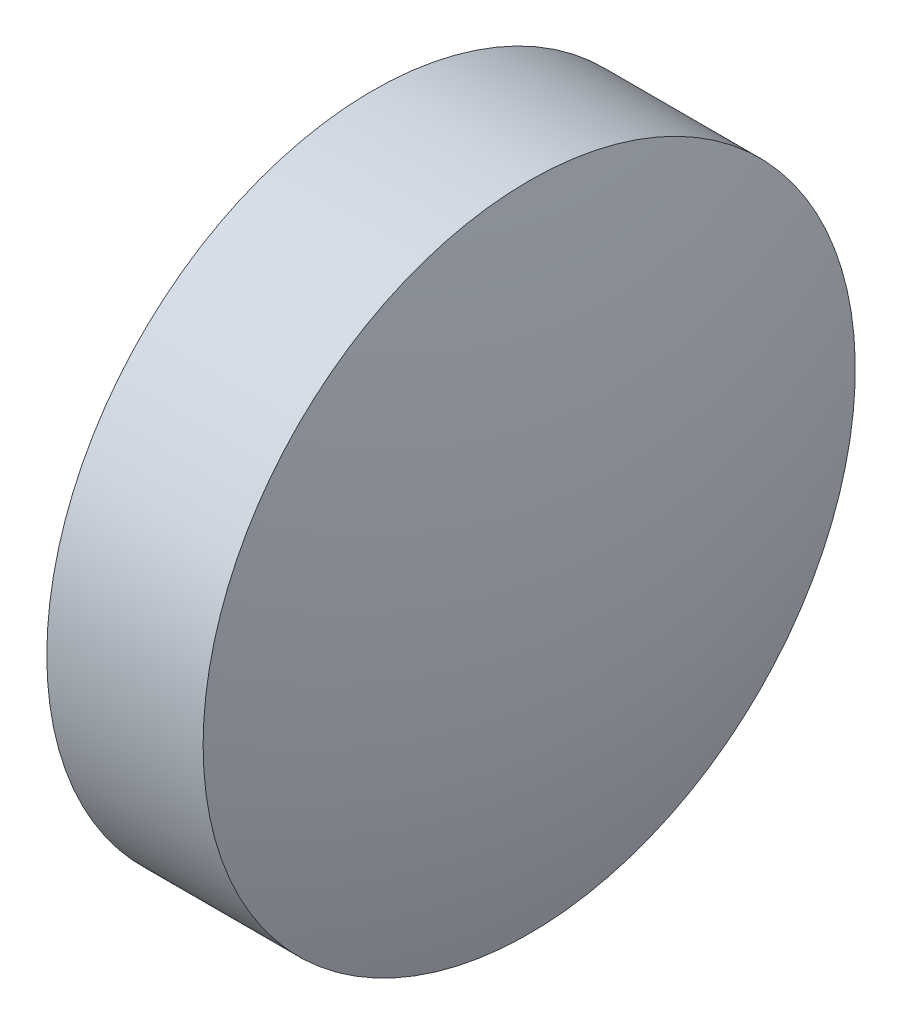
SolidWorks part; units mm, degrees
ref_plane "前视基准面" through (0, 0, 0) normal (0, 0, 1) x (1, 0, 0)
ref_plane "上视基准面" through (0, 0, 0) normal (0, 1, 0) x (1, 0, 0)
ref_plane "右视基准面" through (0, 0, 0) normal (1, 0, 0) x (0, 0, -1)
sketch "草图1" plane through (0, 0, 0) normal (0, 0, 1) x (1, 0, 0)
  line L0 (479.1, 112.7889) -> (532.883, 112.7889) construction
  line L1 (497.5866, 112.7889) -> (497.5866, 115.9389)
  line L2 (497.5866, 112.7889) -> (499.5866, 112.7889)
  line L3 (497.5866, 115.9389) -> (499.0966, 115.9389)
  arc A0 (499.5866, 112.7889) -> (499.0966, 115.9389) centre (489.2166, 112.7889) ccw
revolve "旋转1" add sketch "草图1" angle 360 about L0
